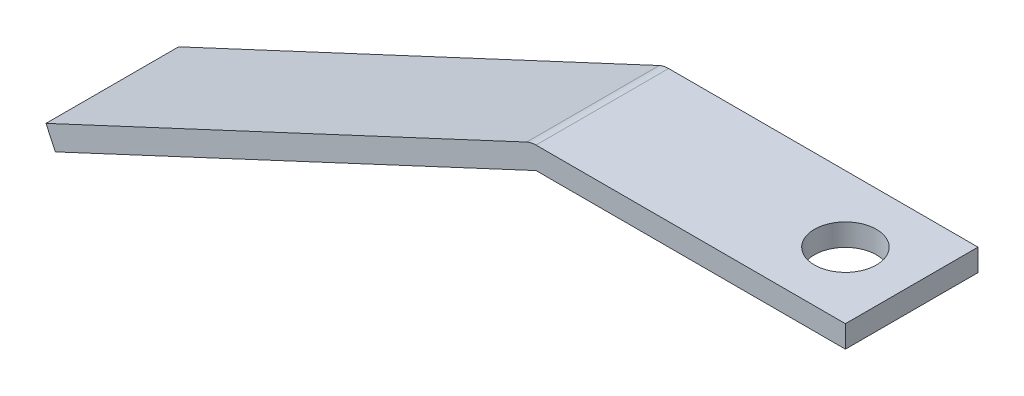
SolidWorks part; units mm, degrees
ref_plane "Front" through (0, 0, 0) normal (0, 0, 1) x (1, 0, 0)
ref_plane "Top" through (0, 0, 0) normal (0, 1, 0) x (1, 0, 0)
ref_plane "Right" through (0, 0, 0) normal (1, 0, 0) x (0, 0, -1)
sketch "Sketch1" plane through (0, 0, 0) normal (0, 0, 1) x (1, 0, 0)
  line L0 (-177.8, 0) -> (-183.1673, 11.5101) construction
  line L1 (0, 0) -> (-177.8, 0)
  line L2 (0, 0) -> (0, 12.7)
  line L3 (0, 12.7) -> (-177.8, 12.7)
  line L4 (-177.8, 0) -> (-177.8, 12.7) construction
  line L5 (-177.8, 0) -> (-454.0426, -128.814)
  line L6 (-183.1673, 11.5101) -> (-459.4099, -117.3039)
  line L7 (-454.0426, -128.814) -> (-459.4099, -117.3039)
  arc A0 (-183.1673, 11.5101) -> (-177.8, 12.7) centre (-177.8, 0) cw
  dimension "D1" = 155
  dimension "D2" = 12.7
  dimension "D3" = 12.7
  dimension "D4" = 304.8
  dimension "D5" = 177.8
extrude "Boss-Extrude1" add sketch "Sketch1" along normal mid plane 76.2
sketch "Sketch2" plane through (0, 12.7, 0) normal (0, 1, 0) x (1, 0, 0)
  line L0 (0, -38.1) -> (0, 38.1) construction
  circle A0 centre (-38.1, 0) radius 17.78
  dimension "D1" = 38.1
  dimension "D2" = 35.56
extrude "Cut-Extrude1" cut sketch "Sketch2" against normal through all
